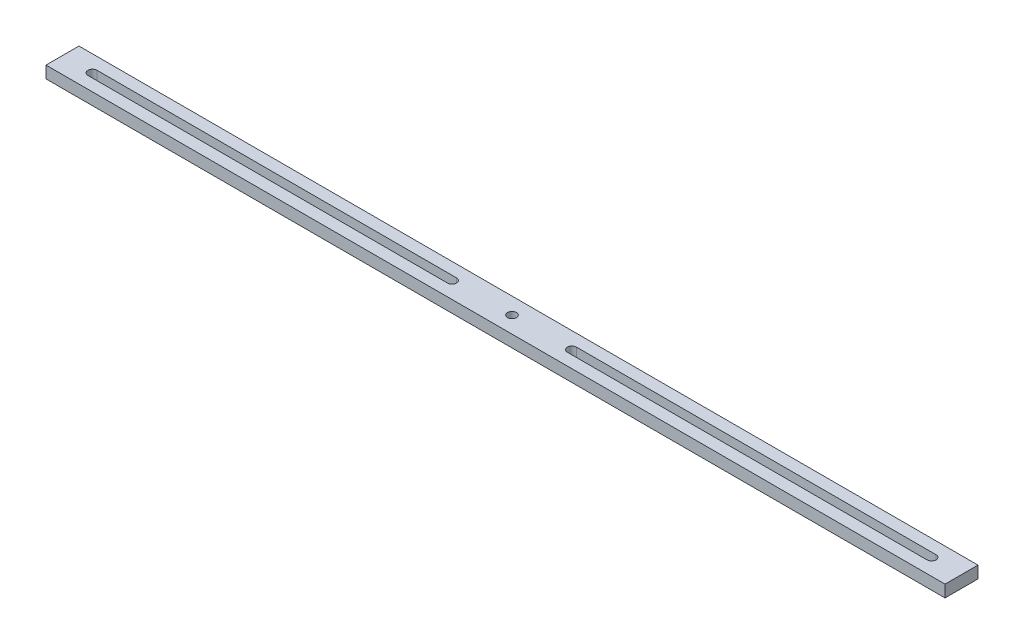
SolidWorks part; units mm, degrees
ref_plane "Front Plane" through (0, 0, 0) normal (0, 0, 1) x (1, 0, 0)
ref_plane "Top Plane" through (0, 0, 0) normal (0, 1, 0) x (1, 0, 0)
ref_plane "Right Plane" through (0, 0, 0) normal (1, 0, 0) x (0, 0, -1)
sketch "Sketch1" plane through (0, 0, 0) normal (0, 1, 0) x (1, 0, 0)
  line L0 (0, -6.05) -> (0, 6.05) construction
  line L5 (0, 0) -> (0, 1.5) construction
  line L6 (-150, 5.5) -> (150, 5.5)
  line L11 (-150, 5.5) -> (-150, -5.5)
  line L12 (-150, -5.5) -> (150, -5.5)
  line L22 (150, 5.5) -> (150, -5.5)
  line L23 (-150, 5.5) -> (150, -5.5) construction
  line L24 (-150, -5.5) -> (150, 5.5) construction
  line L25 (0, 1.5) -> (20, 1.5) construction
  line L26 (20, 1.5) -> (140, 1.5)
  line L28 (20, -1.5) -> (140, -1.5)
  line L30 (-20, -1.5) -> (-140, -1.5)
  line L31 (-20, 1.5) -> (-140, 1.5)
  arc A0 (20, 1.5) -> (20, -1.5) centre (20, 0) ccw
  arc A2 (140, -1.5) -> (140, 1.5) centre (140, 0) ccw
  arc A3 (-140, -1.5) -> (-140, 1.5) centre (-140, 0) cw
  arc A4 (-20, 1.5) -> (-20, -1.5) centre (-20, 0) cw
  circle A5 centre (0, 0) radius 1.5
  point P0 (0, 0)
  dimension "D8" = 3
  dimension "D9" = 3
  dimension "D7" = 3
  dimension "D1" = 11
  dimension "D2" = 300
  dimension "D3" = 1.5
  dimension "D4" = 20
  dimension "D5" = 3
  dimension "D6" = 120
extrude "Boss-Extrude2" add sketch "Sketch1" along normal blind 4
